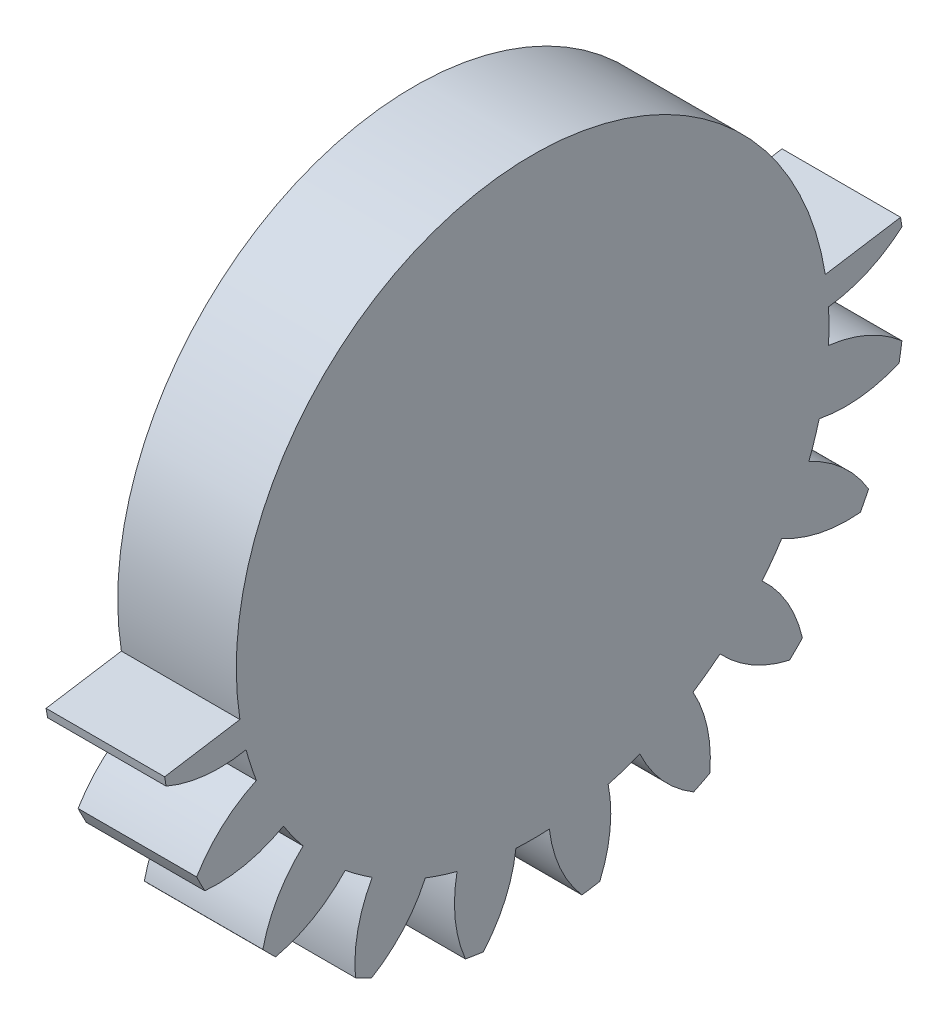
SolidWorks part; units mm, degrees
ref_plane "Plane1" through (0, 0, 0) normal (0, 0, 1) x (1, 0, 0)
ref_plane "Plane2" through (0, 0, 0) normal (0, 1, 0) x (1, 0, 0)
ref_plane "Plane3" through (0, 0, 0) normal (1, 0, 0) x (0, 0, -1)
other "Configuration Table"
sketch "HoldingSke" plane through (0, 0, 0) normal (0, 1, 0) x (1, 0, 0)
  line L0 (0, 0) -> (0.4698, -0.171)
  line L1 (-15, 0) -> (100, 0) construction
  line L2 (0, 0) -> (-2.1039, 2.3779)
  line L3 (0, 0) -> (-11.863, 4.5341)
  line L4 (0, 0) -> (8.1152, 2.9537)
  line L5 (0, 0) -> (-46.8476, -17.4728)
  line L6 (0, 0) -> (-12.4344, -8.3896)
  line L7 (-2.1039, 2.3779) -> (8.6586, 51.2059)
  line L8 (-76.2, 54.61) -> (-76.1, 54.61)
  line L9 (-71.009, 38.7566) -> (-53.1078, 45.2721)
  line L10 (-76.2, 71.12) -> (104.1128, 71.12)
  line L11 (0, 0) -> (-15, 0)
  line L12 (-76.2, 101.6) -> (-76.133, 101.6)
  line L13 (24.9733, 27.94) -> (52.9518, 28.4284)
  line L14 (24.9733, 27.94) -> (24.9743, 27.94)
  line L15 (24.9733, 27.94) -> (100.4006, 29.5858)
  line L16 (-63.627, -2) -> (-12.827, -2)
  circle A0 centre (0, 0) radius 0.5
  circle A1 centre (0, 0) radius 17.499
  circle A2 centre (0, 0) radius 37.5
  circle A3 centre (0, 0) radius 0.5
  dimension "MHD" = 34.998
  dimension "Hub_dia" = 75
  dimension "Bore" = 1
  dimension "MBD" = 1
  dimension "Num_teeth" = 20
  dimension "Pitch" = 0.5
  dimension "Overall_len" = 50
  dimension "Show_teeth" = 20
  dimension "Thickness" = 15
  dimension "OAL" = 50.0001
  dimension "T_dim" = 0.1
  dimension "Ap" = 20
  dimension "H" = 19.05
  dimension "Pitch_radius" = 180.3128
  dimension "Width" = 15
  dimension "Backlash" = 0.067
  dimension "Addendum_fac" = 1
  dimension "Dedendum_fac" = 1.25
  dimension "Clearance_fac" = 0.25
  dimension "Dedendum_add" = 0.001
  dimension "Module" = 2
sketch "BasProSke" plane through (0, 0, 0) normal (0, 1, 0) x (1, 0, 0)
  line L0 (-10, 0) -> (60, 0) construction
  line L1 (0, 0) -> (0, 22)
  line L2 (0, 0) -> (15, 0)
  line L3 (15, 0) -> (15, 22)
  line L4 (15, 22) -> (0, 22)
  dimension "Thickness" = 15
  dimension "Diameter" = 44
revolve "Base-Revolve" add sketch "BasProSke" angle 360 about L0
sketch "TooCutSke" plane through (0, 0, 0) normal (1, 0, 0) x (0, 0, -1)
  line L1 (0, 0) -> (0, 107) construction
  line L2 (0, 0) -> (-1.6864, 19.9288) construction
  line L3 (0, 0) -> (-6.2409, 39.4033) construction
  line L4 (-1.6864, 19.9288) -> (-3.1204, 19.7016) construction
  arc A0 (0.9862, 17.4712) -> (-0.9862, 17.4712) centre (0, 0) ccw
  arc A1 (2.9329, 21.8293) -> (-2.9329, 21.8293) centre (0, 0) ccw
  circle A2 centre (0, 0) radius 20 construction
  circle A3 centre (0, 0) radius 18.7939 construction
  arc A4 (-0.9862, 17.4712) -> (-2.9329, 21.8293) centre (-8.9313, 16.536) ccw
  arc A5 (2.9329, 21.8293) -> (0.9862, 17.4712) centre (8.9313, 16.536) ccw
  dimension "Root_dia" = 34.998
  dimension "Overcut_dia" = 44.0508
  dimension "Pitch_dia" = 40
  dimension "Base_dia" = 37.5877
  dimension "Flank_rad" = 8
  dimension "Half_ang" = 9
  dimension "Half_CT" = 1.4519
extrude "ToothCut" cut sketch "TooCutSke" along normal through all
fillet "Breaks" [suppressed] radius 0.04
fillet "RootFillets" [suppressed] radius 0.501
pattern_circular "TeethCuts" count 20 every 18 about axis through (-10, 0, 0) along (1, 0, 0) of "ToothCut", "RootFillets", "Breaks"
sketch "HubNeaOneSke" plane through (0, 0, 0) normal (-1, 0, 0) x (0, 0, 1)
  circle A0 centre (0, 0) radius 17.499
  dimension "Diameter" = 34.998
extrude "HubNearOne" [suppressed] add sketch "HubNeaOneSke" along normal blind 35.0001
sketch "HubNeaBotSke" plane through (0, 0, 0) normal (-1, 0, 0) x (0, 0, 1)
  circle A0 centre (0, 0) radius 17.499
  dimension "Diameter" = 34.998
extrude "HubNearBoth" [suppressed] add sketch "HubNeaBotSke" along normal blind 17.5
ref_plane "FarPln" through (15, 0, 0) normal (1, 0, 0) x (0, 0, -1)
sketch "HubFarSke" plane through (15, 0, 0) normal (1, 0, 0) x (0, 0, -1)
  circle A0 centre (0, 0) radius 17.499
  dimension "Diameter" = 34.998
extrude "HubFar" [suppressed] add sketch "HubFarSke" along normal blind 17.5
sketch "BorSke" plane through (0, 0, 0) normal (1, 0, 0) x (0, 0, -1)
  circle A0 centre (0, 0) radius 0.5
  dimension "Diameter" = 1
extrude "Bore" cut sketch "BorSke" along normal mid plane 100.0001
sketch "KeySke" plane through (0, 0, 0) normal (1, 0, 0) x (0, 0, -1)
  line L0 (-0.05, 0) -> (-0.05, 0.6)
  line L1 (-0.05, 0.6) -> (0.05, 0.6)
  line L2 (0.05, 0.6) -> (0.05, 0)
  line L3 (0, 0) -> (0, 34) construction
  line L4 (-0.05, 0) -> (0.05, 0)
  dimension "Offset" = 0.6
  dimension "Width" = 0.1
extrude "Keyway" [suppressed] cut sketch "KeySke" along normal mid plane 100.0001
pattern_circular "Keyway2" [suppressed] count 2 every 90 about axis through (-10, 0, 0) along (1, 0, 0)
sketch "Sketch1" plane through (0, 0, 0) normal (-1, 0, 0) x (0, 0, 1)
  circle A0 centre (0, 0) radius 11.1
extrude "Cut-Extrude1" cut sketch "Sketch1" against normal blind 16
sketch "Sketch2" plane through (0, 0, 0) normal (-1, 0, 0) x (0, 0, 1)
  arc A80 (17.4712, 0.9862) -> (21.8063, 2.9127) centre (16.536, 8.9313) ccw
  arc A81 (21.8063, 2.9127) -> (21.6391, 3.9684) centre (0, 0) ccw
  arc A82 (21.6391, 3.9684) -> (16.9208, 4.461) centre (18.4866, -3.3843) ccw
  arc A83 (16.9208, 4.461) -> (16.3113, 6.3368) centre (0, 0) ccw
  arc A84 (16.3113, 6.3368) -> (19.839, 9.5087) centre (12.9668, 13.6041) ccw
  arc A85 (19.839, 9.5087) -> (19.3537, 10.461) centre (0, 0) ccw
  arc A86 (19.3537, 10.461) -> (14.7141, 9.4715) centre (18.6276, 2.494) ccw
  arc A87 (14.7141, 9.4715) -> (13.5548, 11.0671) centre (0, 0) ccw
  arc A88 (13.5548, 11.0671) -> (15.9297, 15.1739) centre (8.1282, 16.9452) ccw
  arc A89 (15.9297, 15.1739) -> (15.1739, 15.9297) centre (0, 0) ccw
  arc A90 (15.1739, 15.9297) -> (11.0671, 13.5548) centre (16.9452, 8.1282) ccw
  arc A91 (11.0671, 13.5548) -> (9.4715, 14.7141) centre (0, 0) ccw
  arc A92 (9.4715, 14.7141) -> (10.461, 19.3537) centre (2.494, 18.6276) ccw
  arc A93 (10.461, 19.3537) -> (9.5087, 19.839) centre (0, 0) ccw
  arc A94 (9.5087, 19.839) -> (6.3368, 16.3113) centre (13.6041, 12.9668) ccw
  arc A95 (6.3368, 16.3113) -> (4.461, 16.9208) centre (0, 0) ccw
  arc A96 (4.461, 16.9208) -> (3.9684, 21.6391) centre (-3.3843, 18.4866) ccw
  arc A97 (3.9684, 21.6391) -> (2.9127, 21.8063) centre (0, 0) ccw
  arc A98 (2.9127, 21.8063) -> (0.9862, 17.4712) centre (8.9313, 16.536) ccw
  arc A99 (0.9862, 17.4712) -> (-0.9862, 17.4712) centre (0, 0) ccw
  arc A100 (-0.9862, 17.4712) -> (-2.9127, 21.8063) centre (-8.9313, 16.536) ccw
  arc A101 (-2.9127, 21.8063) -> (-3.9684, 21.6391) centre (0, 0) ccw
  arc A102 (-3.9684, 21.6391) -> (-4.461, 16.9208) centre (3.3843, 18.4866) ccw
  arc A103 (-4.461, 16.9208) -> (-6.3368, 16.3113) centre (0, 0) ccw
  arc A104 (-6.3368, 16.3113) -> (-9.5087, 19.839) centre (-13.6041, 12.9668) ccw
  arc A105 (-9.5087, 19.839) -> (-10.461, 19.3537) centre (0, 0) ccw
  arc A106 (-10.461, 19.3537) -> (-9.4715, 14.7141) centre (-2.494, 18.6276) ccw
  arc A107 (-9.4715, 14.7141) -> (-11.0671, 13.5548) centre (0, 0) ccw
  arc A108 (-11.0671, 13.5548) -> (-15.1739, 15.9297) centre (-16.9452, 8.1282) ccw
  arc A109 (-15.1739, 15.9297) -> (-15.9297, 15.1739) centre (0, 0) ccw
  arc A110 (-15.9297, 15.1739) -> (-13.5548, 11.0671) centre (-8.1282, 16.9452) ccw
  arc A111 (-13.5548, 11.0671) -> (-14.7141, 9.4715) centre (0, 0) ccw
  arc A112 (-14.7141, 9.4715) -> (-19.3537, 10.461) centre (-18.6276, 2.494) ccw
  arc A113 (-19.3537, 10.461) -> (-19.839, 9.5087) centre (0, 0) ccw
  arc A114 (-19.839, 9.5087) -> (-16.3113, 6.3368) centre (-12.9668, 13.6041) ccw
  arc A115 (-16.3113, 6.3368) -> (-16.9208, 4.461) centre (0, 0) ccw
  arc A116 (-16.9208, 4.461) -> (-21.6391, 3.9684) centre (-18.4866, -3.3843) ccw
  arc A117 (-21.6391, 3.9684) -> (-21.8063, 2.9127) centre (0, 0) ccw
  arc A118 (-21.8063, 2.9127) -> (-17.4712, 0.9862) centre (-16.536, 8.9313) ccw
  arc A119 (-17.4712, 0.9862) -> (-17.4712, -0.9862) centre (0, 0) ccw
  arc A120 (-17.4712, -0.9862) -> (-21.8063, -2.9127) centre (-16.536, -8.9313) ccw
  arc A121 (-21.8063, -2.9127) -> (-21.6391, -3.9684) centre (0, 0) ccw
  arc A122 (-21.6391, -3.9684) -> (-16.9208, -4.461) centre (-18.4866, 3.3843) ccw
  arc A123 (-16.9208, -4.461) -> (-16.3113, -6.3368) centre (0, 0) ccw
  arc A124 (-16.3113, -6.3368) -> (-19.839, -9.5087) centre (-12.9668, -13.6041) ccw
  arc A125 (-19.839, -9.5087) -> (-19.3537, -10.461) centre (0, 0) ccw
  arc A126 (-19.3537, -10.461) -> (-14.7141, -9.4715) centre (-18.6276, -2.494) ccw
  arc A127 (-14.7141, -9.4715) -> (-13.5548, -11.0671) centre (0, 0) ccw
  arc A128 (-13.5548, -11.0671) -> (-15.9297, -15.1739) centre (-8.1282, -16.9452) ccw
  arc A129 (-15.9297, -15.1739) -> (-15.1739, -15.9297) centre (0, 0) ccw
  arc A130 (-15.1739, -15.9297) -> (-11.0671, -13.5548) centre (-16.9452, -8.1282) ccw
  arc A131 (-11.0671, -13.5548) -> (-9.4715, -14.7141) centre (0, 0) ccw
  arc A132 (-9.4715, -14.7141) -> (-10.461, -19.3537) centre (-2.494, -18.6276) ccw
  arc A133 (-10.461, -19.3537) -> (-9.5087, -19.839) centre (0, 0) ccw
  arc A134 (-9.5087, -19.839) -> (-6.3368, -16.3113) centre (-13.6041, -12.9668) ccw
  arc A135 (-6.3368, -16.3113) -> (-4.461, -16.9208) centre (0, 0) ccw
  arc A136 (-4.461, -16.9208) -> (-3.9684, -21.6391) centre (3.3843, -18.4866) ccw
  arc A137 (-3.9684, -21.6391) -> (-2.9127, -21.8063) centre (0, 0) ccw
  arc A138 (-2.9127, -21.8063) -> (-0.9862, -17.4712) centre (-8.9313, -16.536) ccw
  arc A139 (-0.9862, -17.4712) -> (0.9862, -17.4712) centre (0, 0) ccw
  arc A140 (0.9862, -17.4712) -> (2.9127, -21.8063) centre (8.9313, -16.536) ccw
  arc A141 (2.9127, -21.8063) -> (3.9684, -21.6391) centre (0, 0) ccw
  arc A142 (3.9684, -21.6391) -> (4.461, -16.9208) centre (-3.3843, -18.4866) ccw
  arc A143 (4.461, -16.9208) -> (6.3368, -16.3113) centre (0, 0) ccw
  arc A144 (6.3368, -16.3113) -> (9.5087, -19.839) centre (13.6041, -12.9668) ccw
  arc A145 (9.5087, -19.839) -> (10.461, -19.3537) centre (0, 0) ccw
  arc A146 (10.461, -19.3537) -> (9.4715, -14.7141) centre (2.494, -18.6276) ccw
  arc A147 (9.4715, -14.7141) -> (11.0671, -13.5548) centre (0, 0) ccw
  arc A148 (11.0671, -13.5548) -> (15.1739, -15.9297) centre (16.9452, -8.1282) ccw
  arc A149 (15.1739, -15.9297) -> (15.9297, -15.1739) centre (0, 0) ccw
  arc A150 (15.9297, -15.1739) -> (13.5548, -11.0671) centre (8.1282, -16.9452) ccw
  arc A151 (13.5548, -11.0671) -> (14.7141, -9.4715) centre (0, 0) ccw
  arc A152 (14.7141, -9.4715) -> (19.3537, -10.461) centre (18.6276, -2.494) ccw
  arc A153 (19.3537, -10.461) -> (19.839, -9.5087) centre (0, 0) ccw
  arc A154 (19.839, -9.5087) -> (16.3113, -6.3368) centre (12.9668, -13.6041) ccw
  arc A155 (16.3113, -6.3368) -> (16.9208, -4.461) centre (0, 0) ccw
  arc A156 (16.9208, -4.461) -> (21.6391, -3.9684) centre (18.4866, 3.3843) ccw
  arc A157 (21.6391, -3.9684) -> (21.8063, -2.9127) centre (0, 0) ccw
  arc A158 (21.8063, -2.9127) -> (17.4712, -0.9862) centre (16.536, -8.9313) ccw
  arc A159 (17.4712, -0.9862) -> (17.4712, 0.9862) centre (0, 0) ccw
  arc A160 (17.4712, 0.9862) -> (21.8063, 2.9127) centre (16.536, 8.9313) ccw
  arc A161 (21.8063, 2.9127) -> (21.6391, 3.9684) centre (0, 0) ccw
  arc A162 (21.6391, 3.9684) -> (16.9208, 4.461) centre (18.4866, -3.3843) ccw
  arc A163 (16.9208, 4.461) -> (16.3113, 6.3368) centre (0, 0) ccw
  arc A164 (16.3113, 6.3368) -> (19.839, 9.5087) centre (12.9668, 13.6041) ccw
  arc A165 (19.839, 9.5087) -> (19.3537, 10.461) centre (0, 0) ccw
  arc A166 (19.3537, 10.461) -> (14.7141, 9.4715) centre (18.6276, 2.494) ccw
  arc A167 (14.7141, 9.4715) -> (13.5548, 11.0671) centre (0, 0) ccw
  arc A168 (13.5548, 11.0671) -> (15.9297, 15.1739) centre (8.1282, 16.9452) ccw
  arc A169 (15.9297, 15.1739) -> (15.1739, 15.9297) centre (0, 0) ccw
  arc A170 (15.1739, 15.9297) -> (11.0671, 13.5548) centre (16.9452, 8.1282) ccw
  arc A171 (11.0671, 13.5548) -> (9.4715, 14.7141) centre (0, 0) ccw
  arc A172 (9.4715, 14.7141) -> (10.461, 19.3537) centre (2.494, 18.6276) ccw
  arc A173 (10.461, 19.3537) -> (9.5087, 19.839) centre (0, 0) ccw
  arc A174 (9.5087, 19.839) -> (6.3368, 16.3113) centre (13.6041, 12.9668) ccw
  arc A175 (6.3368, 16.3113) -> (4.461, 16.9208) centre (0, 0) ccw
  arc A176 (4.461, 16.9208) -> (3.9684, 21.6391) centre (-3.3843, 18.4866) ccw
  arc A177 (3.9684, 21.6391) -> (2.9127, 21.8063) centre (0, 0) ccw
  arc A178 (2.9127, 21.8063) -> (0.9862, 17.4712) centre (8.9313, 16.536) ccw
  arc A179 (0.9862, 17.4712) -> (-0.9862, 17.4712) centre (0, 0) ccw
  arc A180 (-0.9862, 17.4712) -> (-2.9127, 21.8063) centre (-8.9313, 16.536) ccw
  arc A181 (-2.9127, 21.8063) -> (-3.9684, 21.6391) centre (0, 0) ccw
  arc A182 (-3.9684, 21.6391) -> (-4.461, 16.9208) centre (3.3843, 18.4866) ccw
  arc A183 (-4.461, 16.9208) -> (-6.3368, 16.3113) centre (0, 0) ccw
  arc A184 (-6.3368, 16.3113) -> (-9.5087, 19.839) centre (-13.6041, 12.9668) ccw
  arc A185 (-9.5087, 19.839) -> (-10.461, 19.3537) centre (0, 0) ccw
  arc A186 (-10.461, 19.3537) -> (-9.4715, 14.7141) centre (-2.494, 18.6276) ccw
  arc A187 (-9.4715, 14.7141) -> (-11.0671, 13.5548) centre (0, 0) ccw
  arc A188 (-11.0671, 13.5548) -> (-15.1739, 15.9297) centre (-16.9452, 8.1282) ccw
  arc A189 (-15.1739, 15.9297) -> (-15.9297, 15.1739) centre (0, 0) ccw
  arc A190 (-15.9297, 15.1739) -> (-13.5548, 11.0671) centre (-8.1282, 16.9452) ccw
  arc A191 (-13.5548, 11.0671) -> (-14.7141, 9.4715) centre (0, 0) ccw
  arc A192 (-14.7141, 9.4715) -> (-19.3537, 10.461) centre (-18.6276, 2.494) ccw
  arc A193 (-19.3537, 10.461) -> (-19.839, 9.5087) centre (0, 0) ccw
  arc A194 (-19.839, 9.5087) -> (-16.3113, 6.3368) centre (-12.9668, 13.6041) ccw
  arc A195 (-16.3113, 6.3368) -> (-16.9208, 4.461) centre (0, 0) ccw
  arc A196 (-16.9208, 4.461) -> (-21.6391, 3.9684) centre (-18.4866, -3.3843) ccw
  arc A197 (-21.6391, 3.9684) -> (-21.8063, 2.9127) centre (0, 0) ccw
  arc A198 (-21.8063, 2.9127) -> (-17.4712, 0.9862) centre (-16.536, 8.9313) ccw
  arc A199 (-17.4712, 0.9862) -> (-17.4712, -0.9862) centre (0, 0) ccw
  arc A200 (-17.4712, -0.9862) -> (-21.8063, -2.9127) centre (-16.536, -8.9313) ccw
  arc A201 (-21.8063, -2.9127) -> (-21.6391, -3.9684) centre (0, 0) ccw
  arc A202 (-21.6391, -3.9684) -> (-16.9208, -4.461) centre (-18.4866, 3.3843) ccw
  arc A203 (-16.9208, -4.461) -> (-16.3113, -6.3368) centre (0, 0) ccw
  arc A204 (-16.3113, -6.3368) -> (-19.839, -9.5087) centre (-12.9668, -13.6041) ccw
  arc A205 (-19.839, -9.5087) -> (-19.3537, -10.461) centre (0, 0) ccw
  arc A206 (-19.3537, -10.461) -> (-14.7141, -9.4715) centre (-18.6276, -2.494) ccw
  arc A207 (-14.7141, -9.4715) -> (-13.5548, -11.0671) centre (0, 0) ccw
  arc A208 (-13.5548, -11.0671) -> (-15.9297, -15.1739) centre (-8.1282, -16.9452) ccw
  arc A209 (-15.9297, -15.1739) -> (-15.1739, -15.9297) centre (0, 0) ccw
  arc A210 (-15.1739, -15.9297) -> (-11.0671, -13.5548) centre (-16.9452, -8.1282) ccw
  arc A211 (-11.0671, -13.5548) -> (-9.4715, -14.7141) centre (0, 0) ccw
  arc A212 (-9.4715, -14.7141) -> (-10.461, -19.3537) centre (-2.494, -18.6276) ccw
  arc A213 (-10.461, -19.3537) -> (-9.5087, -19.839) centre (0, 0) ccw
  arc A214 (-9.5087, -19.839) -> (-6.3368, -16.3113) centre (-13.6041, -12.9668) ccw
  arc A215 (-6.3368, -16.3113) -> (-4.461, -16.9208) centre (0, 0) ccw
  arc A216 (-4.461, -16.9208) -> (-3.9684, -21.6391) centre (3.3843, -18.4866) ccw
  arc A217 (-3.9684, -21.6391) -> (-2.9127, -21.8063) centre (0, 0) ccw
  arc A218 (-2.9127, -21.8063) -> (-0.9862, -17.4712) centre (-8.9313, -16.536) ccw
  arc A219 (-0.9862, -17.4712) -> (0.9862, -17.4712) centre (0, 0) ccw
  arc A220 (0.9862, -17.4712) -> (2.9127, -21.8063) centre (8.9313, -16.536) ccw
  arc A221 (2.9127, -21.8063) -> (3.9684, -21.6391) centre (0, 0) ccw
  arc A222 (3.9684, -21.6391) -> (4.461, -16.9208) centre (-3.3843, -18.4866) ccw
  arc A223 (4.461, -16.9208) -> (6.3368, -16.3113) centre (0, 0) ccw
  arc A224 (6.3368, -16.3113) -> (9.5087, -19.839) centre (13.6041, -12.9668) ccw
  arc A225 (9.5087, -19.839) -> (10.461, -19.3537) centre (0, 0) ccw
  arc A226 (10.461, -19.3537) -> (9.4715, -14.7141) centre (2.494, -18.6276) ccw
  arc A227 (9.4715, -14.7141) -> (11.0671, -13.5548) centre (0, 0) ccw
  arc A228 (11.0671, -13.5548) -> (15.1739, -15.9297) centre (16.9452, -8.1282) ccw
  arc A229 (15.1739, -15.9297) -> (15.9297, -15.1739) centre (0, 0) ccw
  arc A230 (15.9297, -15.1739) -> (13.5548, -11.0671) centre (8.1282, -16.9452) ccw
  arc A231 (13.5548, -11.0671) -> (14.7141, -9.4715) centre (0, 0) ccw
  arc A232 (14.7141, -9.4715) -> (19.3537, -10.461) centre (18.6276, -2.494) ccw
  arc A233 (19.3537, -10.461) -> (19.839, -9.5087) centre (0, 0) ccw
  arc A234 (19.839, -9.5087) -> (16.3113, -6.3368) centre (12.9668, -13.6041) ccw
  arc A235 (16.3113, -6.3368) -> (16.9208, -4.461) centre (0, 0) ccw
  arc A236 (16.9208, -4.461) -> (21.6391, -3.9684) centre (18.4866, 3.3843) ccw
  arc A237 (21.6391, -3.9684) -> (21.8063, -2.9127) centre (0, 0) ccw
  arc A238 (21.8063, -2.9127) -> (17.4712, -0.9862) centre (16.536, -8.9313) ccw
  arc A239 (17.4712, -0.9862) -> (17.4712, 0.9862) centre (0, 0) ccw
  dimension "D1" = 0
extrude "Cut-Extrude2" cut sketch "Sketch2" against normal blind 8
sketch "Sketch3" plane through (8, 0, 0) normal (-1, 0, 0) x (0, 0, 1)
  circle A0 centre (0, 0) radius 11.1
extrude "Boss-Extrude1" add sketch "Sketch3" against normal blind 7
sketch "Sketch4" plane through (8, 0, 0) normal (-1, 0, 0) x (0, 0, 1)
  line L0 (21.7291, -3.4416) -> (0, 0)
  line L1 (0, 0) -> (-21.7291, 3.4416)
  line L2 (-21.7291, 3.4416) -> (-17.9799, 27.1136)
  line L3 (-17.9799, 27.1136) -> (25.4784, 20.2305)
  line L4 (25.4784, 20.2305) -> (21.7291, -3.4416)
  arc A0 (21.6391, -3.9684) -> (21.8063, -2.9127) centre (0, 0) ccw construction
  arc A1 (-21.6391, 3.9684) -> (-21.8063, 2.9127) centre (0, 0) ccw construction
extrude "Cut-Extrude3" cut sketch "Sketch4" against normal blind 7
sketch "Sketch5" plane through (8, 0, 0) normal (-1, 0, 0) x (0, 0, 1)
  line L0 (0, 0) -> (-21.7291, 3.4416) construction
  line L1 (-21.7291, 3.4416) -> (21.7291, -3.4416) construction
  line L2 (0, 0) -> (-17.4959, 0.3297) construction
  arc A0 (-17.4712, 0.9862) -> (-17.4712, -0.9862) centre (0, 0) ccw construction
  circle A1 centre (0, 0) radius 17.499
  dimension "D1" = 7.921
extrude "Boss-Extrude2" add sketch "Sketch5" against normal blind 7
equation "' \"Module@HoldingSke\" = 6.35"
equation "' \"Num_teeth@HoldingSke\" = 12"
equation "' \"Ap@HoldingSke\" =  20"
equation "' \"Ap@HoldingSke\" = 20"
equation "' \"Width@HoldingSke\" = 0.5 * 25.4"
equation "' \"Hub_dia@HoldingSke\"= 1 * 25.4"
equation "' \"Hub_dia@HoldingSke\" = 1 * 25.4"
equation "' \"Overall_len@HoldingSke\" = 1.0 * 25.4"
equation "' \"Bore@HoldingSke\" = 0.75 * 25.4"
equation "' \"T_dim@HoldingSke\" = 0.1 * 25.4"
equation "' \"Width@KeySke\" = 0.25 * 25.4"
equation "' \"Show_teeth@HoldingSke\" = 13"
equation "' \"Backlash@HoldingSke\" = 0.009 * 25.4"
equation "' \"Addendum_fac@HoldingSke\" = 1.0"
equation "' \"Dedendum_fac@HoldingSke\" = 1.25"
equation "' \"Dedendum_add@HoldingSke\" = 0.00005 * 25.4"
equation "' \"Clearance_fac@HoldingSke\" = 0.25"
equation "\"Pitch@HoldingSke\" = 1 / \"Module@HoldingSke\""
equation "\"Overcut_dia@TooCutSke\" = (\"Num_teeth@HoldingSke\" + 2 * \"Addendum_fac@HoldingSke\") / \"Pitch@HoldingSke\" + 0.002 * 25.4"
equation "\"Pitch_dia@TooCutSke\" = \"Num_teeth@HoldingSke\" / \"Pitch@HoldingSke\""
equation "\"Base_dia@TooCutSke\" = \"Num_teeth@HoldingSke\" / \"Pitch@HoldingSke\" * cos((\"Ap@HoldingSke\"  * 3.14159265 / 180))"
equation "\"Root_dia@TooCutSke\" = (\"Num_teeth@HoldingSke\" + 2) / \"Pitch@HoldingSke\" - 2 * (\"Addendum_fac@HoldingSke\" + \"Dedendum_fac@HoldingSke\") / \"Pitch@HoldingSke\" - \"Dedendum_add@HoldingSke\" * 2"
equation "\"Half_ang@TooCutSke\" = 180 / \"Num_teeth@HoldingSke\""
equation "\"Half_CT@TooCutSke\" = \"Num_teeth@HoldingSke\" / \"Pitch@HoldingSke\" * sin((3.14159265 / 2 / \"Num_teeth@HoldingSke\")) / 2 - 7 * \"Backlash@HoldingSke\" / 4"
equation "\"Flank_rad@TooCutSke\" = \"Num_teeth@HoldingSke\" / \"Pitch@HoldingSke\" / 5"
equation "\"Radius@RootFillets\" = \"Clearance_fac@HoldingSke\" / \"Pitch@HoldingSke\" + \"Dedendum_add@HoldingSke\""
equation "\"Break_rad@Breaks\" = 0.02 / \"Pitch@HoldingSke\""
equation "\"Thickness@HoldingSke\" = \"Width@HoldingSke\""
equation "\"OAL@HoldingSke\" = \"Thickness@HoldingSke\""
equation "\"MHD@HoldingSke\" = (\"Num_teeth@HoldingSke\" + 2) / \"Pitch@HoldingSke\" - 2 * (\"Addendum_fac@HoldingSke\" + \"Dedendum_fac@HoldingSke\")  / \"Pitch@HoldingSke\" - \"Dedendum_add@HoldingSke\" * 2"
equation "\"MBD@HoldingSke\" = (\"Num_teeth@HoldingSke\" + 2) / \"Pitch@HoldingSke\" - 2 * (\"Addendum_fac@HoldingSke\" + \"Dedendum_fac@HoldingSke\")  / \"Pitch@HoldingSke\" - \"Dedendum_add@HoldingSke\" * 2 - 0.002 * 25.4"
equation "\"MHD@HoldingSke\" = ((sgn( \"MHD@HoldingSke\" - \"Hub_dia@HoldingSke\" )-1)*( \"MHD@HoldingSke\" - \"Hub_dia@HoldingSke\" ))/-2+ \"Hub_dia@HoldingSke\""
equation "\"MBD@HoldingSke\" = ((sgn( \"MBD@HoldingSke\" - \"Bore@HoldingSke\" )-1)*( \"MBD@HoldingSke\" - \"Bore@HoldingSke\" ))/-2+ \"Bore@HoldingSke\""
equation "\"OAL@HoldingSke\" = ((sgn( \"OAL@HoldingSke\" - \"Overall_len@HoldingSke\" )+1)*( \"OAL@HoldingSke\" - \"Overall_len@HoldingSke\" ))/2 + \"Overall_len@HoldingSke\" + 0.000002 * 25.4"
equation "\"Num_teeth@TeethCuts\" = int( \"Show_teeth@HoldingSke\" ) + 1"
equation "\"Num_teeth@TeethCuts\" = ((sgn( \"Num_teeth@TeethCuts\" - \"Num_teeth@HoldingSke\" )-1)*( \"Num_teeth@TeethCuts\" - \"Num_teeth@HoldingSke\" ))/-2+ \"Num_teeth@HoldingSke\""
equation "\"Num_teeth@TeethCuts\" = ((sgn( \"Num_teeth@TeethCuts\" - 2.0)+1)*( \"Num_teeth@TeethCuts\" - 2.0))/2 +2.0"
equation "\"Angle@TeethCuts\" = 360.0 / \"Num_teeth@HoldingSke\""
equation "\"Diameter@BasProSke\" = (\"Num_teeth@HoldingSke\" + 2 * \"Addendum_fac@HoldingSke\") / \"Pitch@HoldingSke\""
equation "\"Thickness@BasProSke\"  = \"Thickness@HoldingSke\""
equation "' \"Fillet_rad@BasProSke\" =  \"Thickness@HoldingSke\" * 0.05"
equation "' \"Fillet_rad@BasProSke\" = \"Thickness@HoldingSke\" * 0.05"
equation "\"MHD@HoldingSke\" = ((sgn( \"MHD@HoldingSke\" - \"Root_dia@TooCutSke\" )-1)*( \"MHD@HoldingSke\" - \"Root_dia@TooCutSke\" ))/-2+ \"Root_dia@TooCutSke\""
equation "\"Diameter@HubNeaOneSke\" = \"MHD@HoldingSke\""
equation "\"Length@HubNearOne\" = \"OAL@HoldingSke\" - \"Thickness@BasProSke\""
equation "\"Diameter@HubNeaBotSke\" = \"MHD@HoldingSke\""
equation "\"Length@HubNearBoth\" = ( \"OAL@HoldingSke\" - \"Thickness@BasProSke\" ) / 2.0"
equation "\"Thickness@FarPln\" = \"Thickness@BasProSke\""
equation "\"Diameter@HubFarSke\" = \"MHD@HoldingSke\""
equation "\"Length@HubFar\" = ( \"OAL@HoldingSke\" - \"Thickness@BasProSke\" ) / 2.0"
equation "\"Diameter@BorSke\" = \"MBD@HoldingSke\""
equation "\"D1@Bore\" = \"OAL@HoldingSke\" * 2.0"
equation "\"D1@Keyway\" = \"OAL@HoldingSke\" * 2.0"
equation "\"Offset@KeySke\" = \"T_dim@HoldingSke\" + \"MBD@HoldingSke\" / 2.0"
